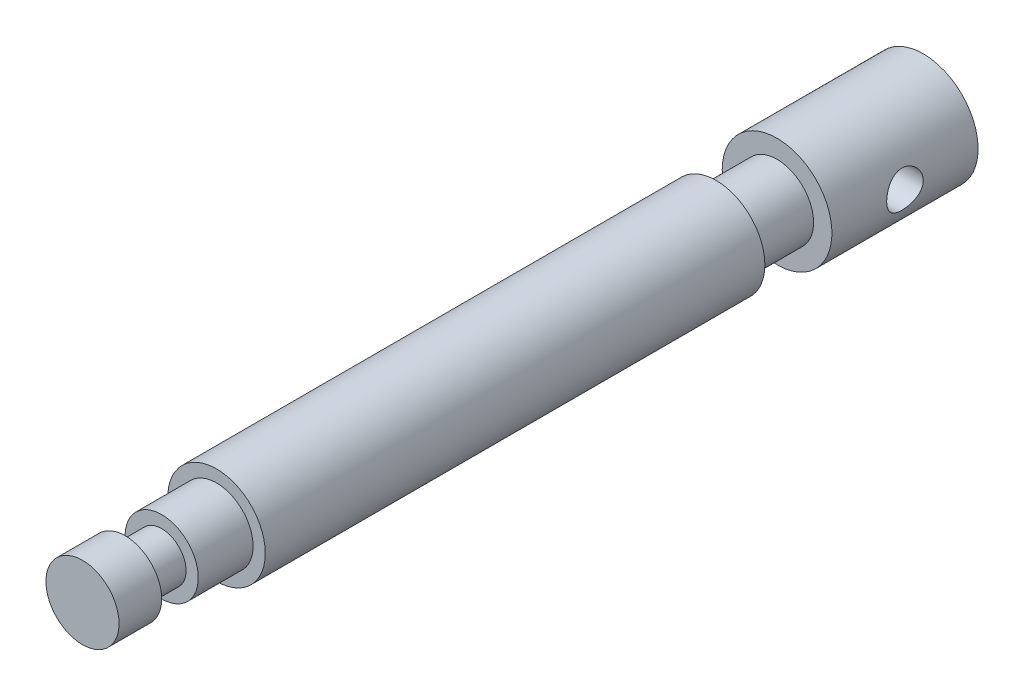
SolidWorks part; units mm, degrees
ref_plane "Front Plane" through (0, 0, 0) normal (0, 0, 1) x (1, 0, 0)
ref_plane "Top Plane" through (0, 0, 0) normal (0, 1, 0) x (1, 0, 0)
ref_plane "Right Plane" through (0, 0, 0) normal (1, 0, 0) x (0, 0, -1)
sketch "Sketch4" plane through (0, 0, 0) normal (0, 0, 1) x (1, 0, 0)
  circle A0 centre (0, 0) radius 8
  dimension "D1" = 16
extrude "Boss-Extrude2" add sketch "Sketch4" along normal mid plane 82
sketch "Sketch5" plane through (0, 0, -41) normal (0, 0, -1) x (-1, 0, 0)
  circle A0 centre (0, 0) radius 6
  dimension "D1" = 12
extrude "Boss-Extrude3" add sketch "Sketch5" along normal blind 10
sketch "Sketch6" plane through (0, 0, -51) normal (0, 0, -1) x (-1, 0, 0)
  circle A0 centre (0, 0) radius 9
  dimension "D1" = 18
extrude "Boss-Extrude4" add sketch "Sketch6" along normal blind 24
sketch "Sketch7" plane through (0, 0, 41) normal (0, 0, 1) x (1, 0, 0)
  circle A0 centre (0, 0) radius 6
  dimension "D1" = 12
extrude "Boss-Extrude5" add sketch "Sketch7" along normal blind 9
sketch "Sketch8" plane through (0, 0, 50) normal (0, 0, 1) x (1, 0, 0)
  circle A0 centre (0, 0) radius 4
  dimension "D1" = 8
extrude "Boss-Extrude6" add sketch "Sketch8" along normal blind 6
sketch "Sketch9" plane through (0, 0, 56) normal (0, 0, 1) x (1, 0, 0)
  circle A0 centre (0, 0) radius 6
  dimension "D1" = 12
extrude "Boss-Extrude7" add sketch "Sketch9" along normal blind 7
sketch "Sketch10" plane through (0, 0, 0) normal (1, 0, 0) x (0, 0, -1)
  line L0 (75, -9) -> (75, 9) construction
  circle A0 centre (63, 0) radius 3
  dimension "D1" = 6
  dimension "D2" = 12
extrude "Cut-Extrude1" cut sketch "Sketch10" against normal mid plane 50
